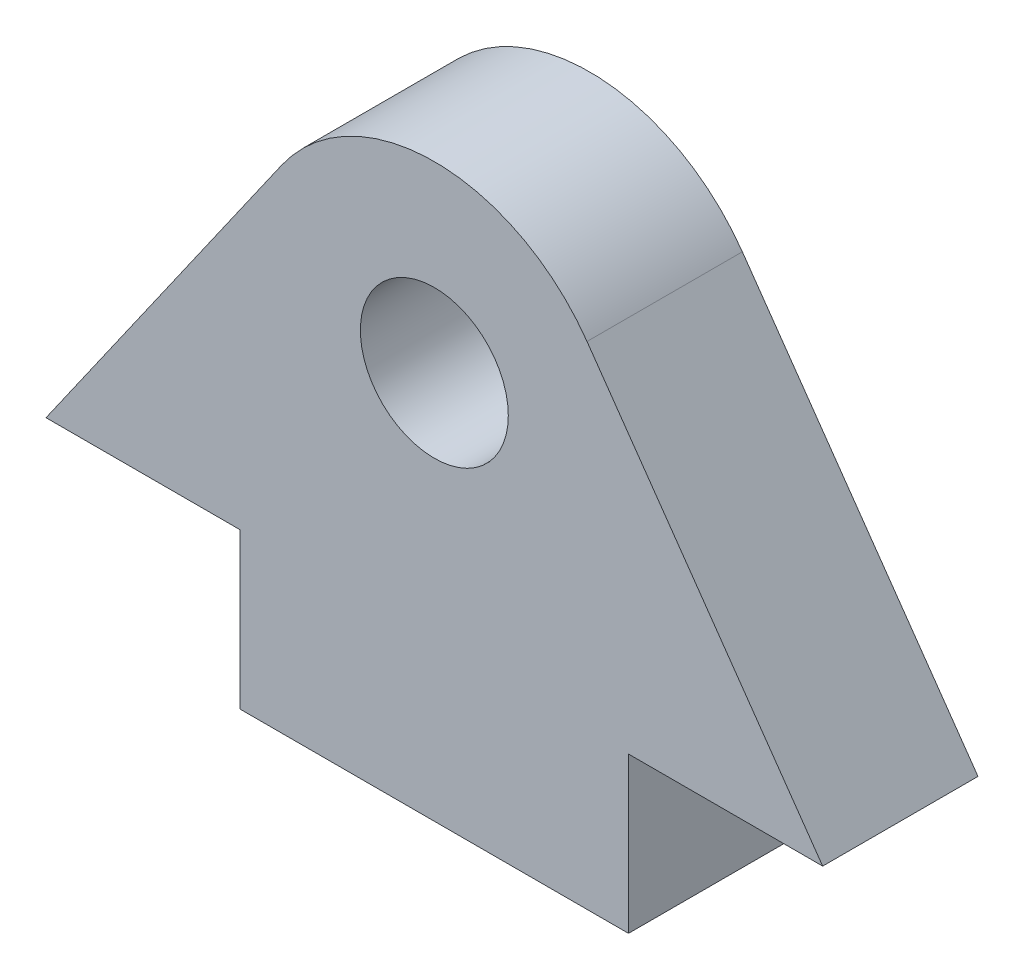
SolidWorks part; units mm, degrees
ref_plane "Front Plane" through (0, 0, 0) normal (0, 0, 1) x (1, 0, 0)
ref_plane "Top Plane" through (0, 0, 0) normal (0, 1, 0) x (1, 0, 0)
ref_plane "Right Plane" through (0, 0, 0) normal (1, 0, 0) x (0, 0, -1)
sketch "Sketch1" plane through (0, 0, 0) normal (0, 0, 1) x (1, 0, 0)
  line L0 (0, 0) -> (50, 0)
  line L1 (50, 0) -> (25, 35.7037)
  line L2 (25, 35.7037) -> (0, 0)
  line L3 (12.5, 0) -> (12.5, -10)
  line L4 (12.5, -10) -> (37.5, -10)
  line L5 (37.5, -10) -> (37.5, 0)
  circle A0 centre (25, 15) radius 4.7625
  dimension "D5" = 9.525
  dimension "D1" = 50
  dimension "D2" = 70
  dimension "D3" = 25
  dimension "D4" = 15
  dimension "D6" = 10
  dimension "D7" = 25
  dimension "D8" = 12.5
  dimension "D9" = 25
  dimension "D10" = 45.7037
  dimension "D11" = 43.5862
extrude "Boss-Extrude1" add sketch "Sketch1" along normal blind 10 contours L1 L2 L0 A0 | L4 L5 L0 L3
fillet "Fillet1" radius 12 1 edges at (25, 35.7037, 5)
